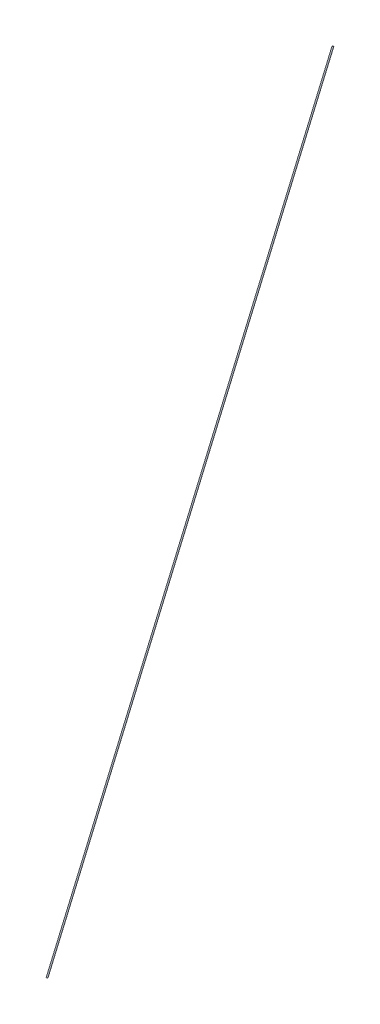
SolidWorks part; units mm, degrees
ref_plane "前视基准面" through (0, 0, 0) normal (0, 0, 1) x (1, 0, 0)
ref_plane "上视基准面" through (0, 0, 0) normal (0, 1, 0) x (1, 0, 0)
ref_plane "右视基准面" through (0, 0, 0) normal (1, 0, 0) x (0, 0, -1)
sketch "草图1" plane through (0, 0, 0) normal (0, 1, 0) x (1, 0, 0)
  line L0 (0, 0) -> (0, -217.5)
sketch "草图2" plane through (0, 0, 0) normal (0, 0, 1) x (1, 0, 0)
  line L0 (0, 0) -> (0, 500)
sketch "草图3" plane through (0, 0, 0) normal (1, 0, 0) x (0, 0, -1)
  line L2 (0, 0) -> (-217.5, 0) construction
  line L5 (0, 0) -> (0, 500) construction
  line L6 (0, 505) -> (-217.5, 0)
sweep "扫描2" add path "草图3" circular profile diameter 1 parameters "D3"=1
